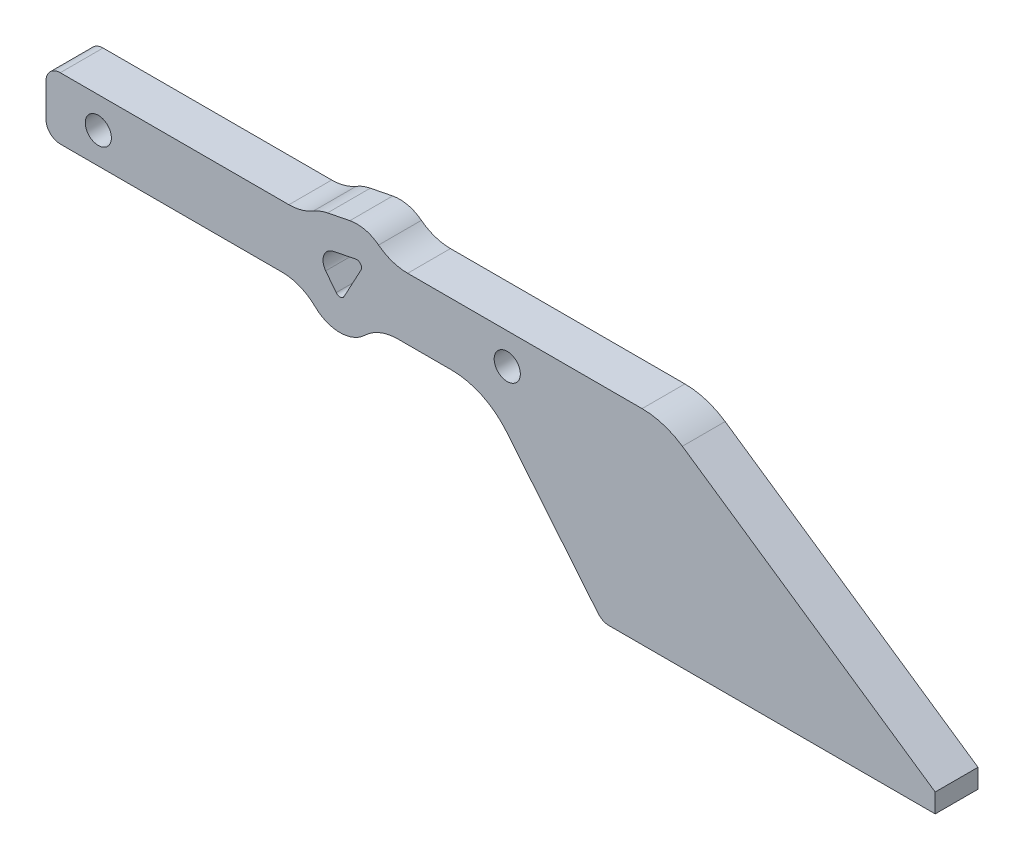
SolidWorks part; units mm, degrees
ref_plane "Front Plane" through (0, 0, 0) normal (0, 0, 1) x (1, 0, 0)
ref_plane "Top Plane" through (0, 0, 0) normal (0, 1, 0) x (1, 0, 0)
ref_plane "Right Plane" through (0, 0, 0) normal (1, 0, 0) x (0, 0, -1)
sketch "Sketch3" plane through (0, 0, 0) normal (0, 0, 1) x (1, 0, 0)
  line L6 (0, 0) -> (-70, 0)
  line L7 (-70, 0) -> (-70, 30) construction
  line L9 (-15.5885, 13) -> (-57, 13) construction
  line L15 (-57, 42.3999) -> (-57, 43) construction
  line L16 (-57, 43) -> (-187, 43)
  line L18 (-90, 30) -> (-90, 43) construction
  line L19 (-90, 36.5) -> (-90, -3.5) construction
  line L20 (-90, -3.5) -> (-126, -3.5) construction
  line L21 (-126, -3.5) -> (-126, 36.5) construction
  line L22 (-125.9771, 31.9631) -> (-128.1788, 34.8221)
  line L23 (-187, 43) -> (-187, 30)
  line L24 (-90, 36.5) -> (-166, 36.5) construction
  line L25 (0, 0) -> (0, 4)
  line L26 (0, 4) -> (-15.5885, 13) construction
  line L27 (-121.8314, 40.1288) -> (-126.5341, 39.1976)
  line L28 (0, 13) -> (-57, 13) construction
  line L29 (-120.7571, 38.673) -> (-124.3048, 32.0984)
  line L30 (-115.0367, 35.5862) -> (-118.5844, 29.0117)
  line L31 (-131.127, 27.9972) -> (-133.3287, 30.8562)
  line L32 (-123.0939, 46.505) -> (-127.7967, 45.5738)
  line L35 (-57, 13) -> (-57, 42.3999) construction
  line L36 (-57, 13) -> (-57, 43) construction
  line L37 (-70, 30) -> (-90, 30) construction
  line L38 (-70, 30) -> (-187, 30) construction
  line L39 (-57, 43) -> (0, 4)
  line L41 (-104.1425, 30) -> (-113.8462, 30) construction
  line L42 (-113.8462, 30) -> (-187, 30)
  line L43 (-113.8462, 30) -> (-94.6383, 30)
  line L44 (-94.6383, 30) -> (-70, 0)
  circle A0 centre (-90, 36.5) radius 2.75
  arc A1 (-126.5341, 39.1976) -> (-128.1788, 34.8221) centre (-126, 36.5) ccw
  circle A5 centre (-166, 36.5) radius 2.75 construction
  circle A6 centre (-176, 36.5) radius 2.75
  arc A8 (-115.3263, 35.0496) -> (-104.1425, 30) centre (-126, -3.5) ccw construction
  arc A9 (-125.9771, 31.9631) -> (-124.3048, 32.0984) centre (-125.1848, 32.5733) ccw
  arc A10 (-121.8314, 40.1288) -> (-120.7571, 38.673) centre (-121.6371, 39.1478) cw
  arc A11 (-131.127, 27.9972) -> (-118.5844, 29.0117) centre (-125.1848, 32.5733) ccw
  arc A12 (-127.7967, 45.5738) -> (-133.3287, 30.8562) centre (-126, 36.5) ccw
  arc A13 (-123.0939, 46.505) -> (-115.0367, 35.5862) centre (-121.6371, 39.1478) cw
  arc A14 (-104.1425, 30) -> (-115.3263, 35.0496) centre (-126, -3.5) ccw construction
  circle A15 centre (-186, 36.5) radius 2.75 [skipped]
  dimension "D7" = 40
  dimension "D8" = 130
  dimension "D12" = 70
  dimension "D3" = 5.5
  dimension "D14" = 2.75
  dimension "D15" = 1
  dimension "D19" = 86
  dimension "D1" = 13
  dimension "D2" = 20
  dimension "D4" = 40
  dimension "D5" = 36
  dimension "D9" = 30
  dimension "D10" = 4
  dimension "D11" = 120
  dimension "D13" = 52.4
  dimension "D6" = 11.2
  dimension "D16" = 10
  dimension "D17" = 6.5
  dimension "D18" = 3
extrude "Boss-Extrude3" add sketch "Sketch3" along normal mid plane 9
fillet "Fillet13" radius 15 2 edges at (-57, 43, 0) (-94.6383, 30, 0)
fillet "Fillet14" radius 10 4 edges at (-115.202, 43, 0) (-132.5812, 43, 0) (-132.6693, 30, 0) (-118.0511, 30, 0)
fillet "Fillet15" radius 3 3 edges at (-70, 0, 0) (-187, 43, 0) (-187, 30, 0)
